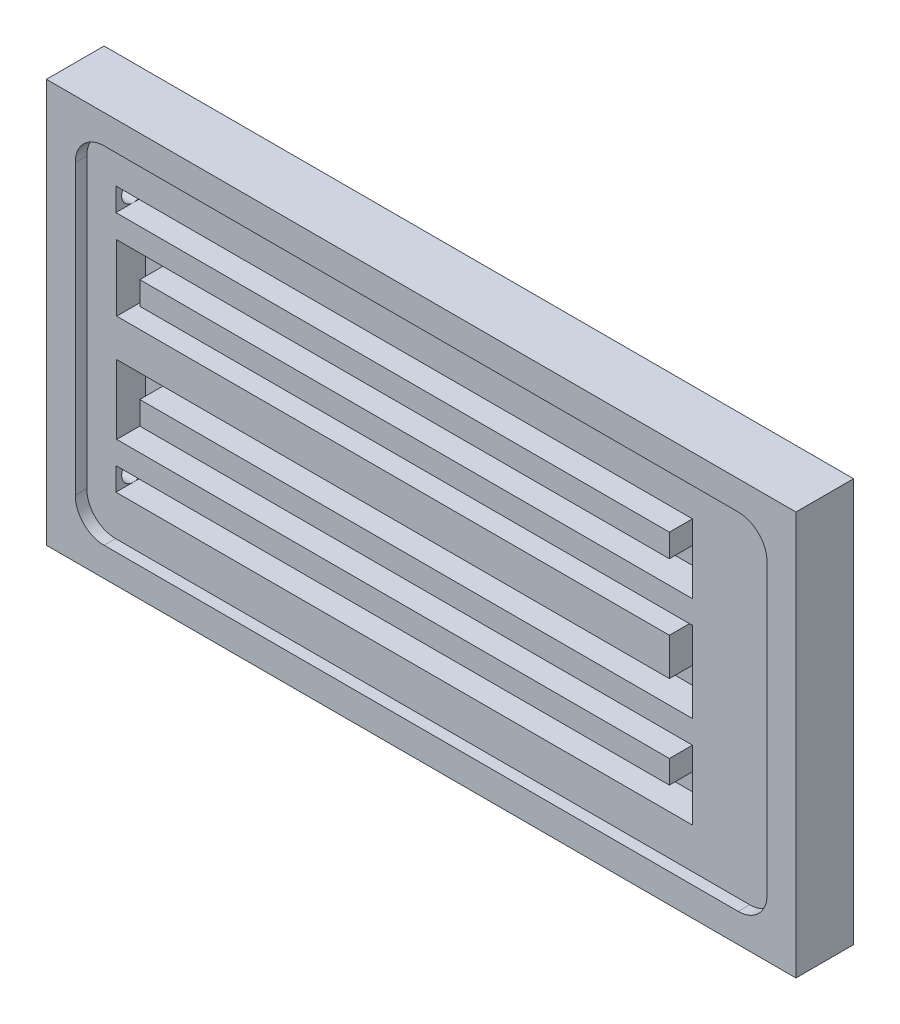
SolidWorks part; units mm, degrees
ref_plane "Plan de face" through (0, 0, 0) normal (0, 0, 1) x (1, 0, 0)
ref_plane "Plan de dessus" through (0, 0, 0) normal (0, 1, 0) x (1, 0, 0)
ref_plane "Plan de droite" through (0, 0, 0) normal (1, 0, 0) x (0, 0, -1)
sketch "Esquisse1" plane through (0, 0, 0) normal (0, 0, 1) x (1, 0, 0)
  line L1 (0, 0) -> (130, 0)
  line L2 (0, 0) -> (0, 70)
  line L3 (0, 70) -> (130, 70)
  line L4 (130, 0) -> (130, 70)
  dimension "D1" = 130
  dimension "D2" = 70
extrude "Boss.-Extru.1" add sketch "Esquisse1" along normal blind 10
sketch "Esquisse18" plane through (0, 0, 10) normal (0, 0, 1) x (1, 0, 0)
  line L0 (130, 70) -> (0, 70) construction
  line L1 (10, 5) -> (120, 5)
  line L2 (5, 10) -> (5, 60)
  line L3 (10, 65) -> (120, 65)
  line L4 (125, 10) -> (125, 60)
  line L5 (130, 0) -> (130, 70) construction
  line L6 (0, 70) -> (0, 0) construction
  line L7 (0, 0) -> (130, 0) construction
  arc A0 (120, 65) -> (125, 60) centre (120, 60) cw
  arc A1 (120, 5) -> (125, 10) centre (120, 10) ccw
  arc A2 (10, 5) -> (5, 10) centre (10, 10) cw
  arc A3 (5, 60) -> (10, 65) centre (10, 60) cw
  dimension "D5" = 5
  dimension "D1" = 5
  dimension "D2" = 5
  dimension "D3" = 5
  dimension "D4" = 5
extrude "Enlèv. mat.-Extru.1" cut sketch "Esquisse18" against normal blind 2
sketch "Esquisse2" plane through (0, 0, 10) normal (0, 0, 1) x (1, 0, 0)
  line L0 (-7.0372, 56) -> (108.0501, 56)
  line L1 (108.0501, 56) -> (108.0501, 48)
  line L2 (108.0501, 14) -> (-7.0372, 14)
  line L3 (108.0501, 48) -> (12.1918, 48)
  line L4 (12.1918, 48) -> (12.1918, 40)
  line L5 (12.1918, 40) -> (108.0501, 40)
  line L6 (108.0501, 40) -> (108.0501, 30)
  line L7 (108.0501, 30) -> (12.1918, 30)
  line L8 (12.1918, 30) -> (12.1918, 22)
  line L9 (12.1918, 22) -> (108.0501, 22)
  line L10 (108.0501, 22) -> (108.0501, 14)
  line L11 (-10.6876, 35) -> (142.6354, 35) construction
  line L12 (0, 0) -> (130, 0) construction
  dimension "D1" = 8
  dimension "D2" = 10
  dimension "D3" = 8
  dimension "D4" = 8
  dimension "D5" = 8
  dimension "D6" = 35
  dimension "D7" = 5
sketch "Esquisse19" plane through (0, 0, 0) normal (-1, 0, 0) x (0, 0, 1)
  circle A0 centre (5, 56) radius 2
  circle A1 centre (5, 14) radius 2
extrude "Enlèv. mat.-Extru.2" cut sketch "Esquisse19" against normal blind 20
sketch "Esquisse20" plane through (0, 0, 8) normal (0, 0, 1) x (1, 0, 0)
  line L0 (10.0501, 58) -> (110.0501, 58)
  line L1 (110.0501, 58) -> (110.0501, 46)
  line L2 (110.0501, 46) -> (14.1918, 46)
  line L3 (14.1918, 46) -> (14.1918, 42)
  line L4 (14.1918, 42) -> (110.0501, 42)
  line L5 (110.0501, 42) -> (110.0501, 28)
  line L6 (110.0501, 28) -> (14.1918, 28)
  line L7 (14.1918, 28) -> (14.1918, 24)
  line L8 (14.1918, 24) -> (110.0501, 24)
  line L9 (110.0501, 24) -> (110.0501, 12)
  line L10 (110.0501, 12) -> (10.0501, 12)
  line L11 (10.0501, 12) -> (10.0501, 16)
  line L12 (10.0501, 16) -> (106.0501, 16)
  line L13 (106.0501, 16) -> (106.0501, 20)
  line L14 (106.0501, 20) -> (10.1918, 20)
  line L15 (10.1918, 20) -> (10.1918, 32)
  line L16 (10.1918, 32) -> (106.0501, 32)
  line L17 (106.0501, 32) -> (106.0501, 38.512)
  line L18 (106.0501, 38.512) -> (10.1918, 38.512)
  line L19 (10.1918, 38.512) -> (10.1918, 50)
  line L20 (10.1918, 50) -> (106.0501, 50)
  line L21 (106.0501, 50) -> (106.0501, 54)
  line L22 (106.0501, 54) -> (10.0501, 54)
  line L23 (10.0501, 54) -> (10.0501, 58)
  line L25 (108.0501, 40) -> (108.0501, 30) construction
  line L26 (108.0501, 30) -> (12.1918, 30) construction
  line L27 (12.1918, 22) -> (108.0501, 22) construction
  line L28 (108.0501, 56) -> (108.0501, 48) construction
  line L29 (108.0501, 48) -> (12.1918, 48) construction
  line L30 (-7.0372, 56) -> (108.0501, 56) construction
  line L31 (12.1918, 48) -> (12.1918, 40) construction
  line L32 (12.1918, 40) -> (108.0501, 40) construction
  line L34 (108.0501, 22) -> (108.0501, 14) construction
  line L35 (12.1918, 30) -> (12.1918, 22) construction
  line L36 (108.0501, 14) -> (-7.0372, 14) construction
  point P25 (0, 0)
  point P26 (106.1913, 38.4769)
  point P33 (10.0501, 56)
  point P40 (0, 0)
  point P41 (10.1202, 58)
  dimension "D1" = 2
  dimension "D2" = 2
  dimension "D3" = 2
  dimension "D4" = 2
  dimension "D5" = 2
  dimension "D6" = 2
  dimension "D7" = 100
  dimension "D8" = 2
  dimension "D9" = 100
  dimension "D10" = 2
  dimension "D11" = 2
  dimension "D12" = 2
  dimension "D13" = 2
  dimension "D14" = 2
  dimension "D15" = 2
  dimension "D16" = 2
  dimension "D17" = 2
  dimension "D18" = 2
  dimension "D19" = 2
  dimension "D20" = 2
  dimension "D21" = 2
  dimension "D22" = 2
  dimension "D23" = 2
extrude "Enlèv. mat.-Extru.3" cut sketch "Esquisse20" against normal blind 5
